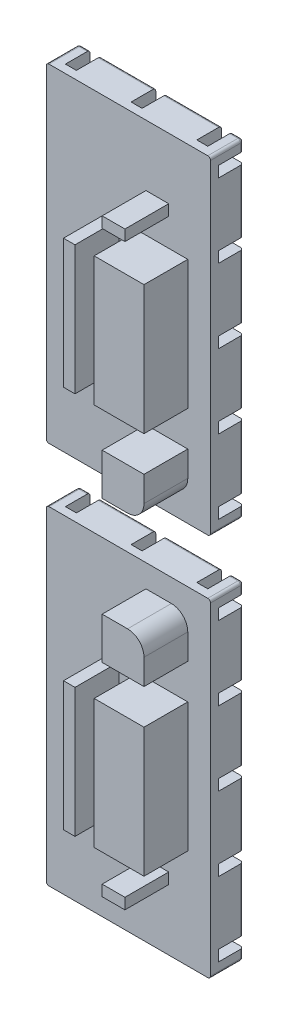
SolidWorks part; units mm, degrees
ref_plane "Front Plane" through (0, 0, 0) normal (0, 0, 1) x (1, 0, 0)
ref_plane "Top Plane" through (0, 0, 0) normal (0, 1, 0) x (1, 0, 0)
ref_plane "Right Plane" through (0, 0, 0) normal (1, 0, 0) x (0, 0, -1)
sketch "Sketch1" plane through (0, 0, 0) normal (0, 0, 1) x (1, 0, 0)
  line L1 (0, 0) -> (30, 0)
  line L2 (0, 0) -> (0, 60)
  line L3 (0, 60) -> (30, 60)
  line L4 (30, 0) -> (30, 60)
  dimension "D1" = 30
  dimension "D2" = 60
extrude "cover" add sketch "Sketch1" along normal blind 6
sketch "Sketch2" plane through (0, 0, 6) normal (0, 0, 1) x (1, 0, 0)
  line L0 (30, 60) -> (0, 60) construction
  line L1 (11.15, 55.85) -> (25.85, 55.85)
  line L2 (11.15, 55.85) -> (11.15, 11.15)
  line L3 (11.15, 11.15) -> (25.85, 11.15)
  line L4 (25.85, 55.85) -> (25.85, 11.15)
  line L6 (0, 0) -> (30, 0) construction
  line L7 (30, 0) -> (30, 60) construction
  line L8 (0, 60) -> (0, 0) construction
  dimension "D1" = 4.15
  dimension "D3" = 11.15
  dimension "D2" = 4.15
  dimension "D4" = 11.15
extrude "plug" add sketch "Sketch2" along normal blind 8
sketch "Sketch3" plane through (0, 0, 0) normal (0, 0, -1) x (-1, 0, 0)
  line L8 (0, 0) -> (-30, 0) construction
  line L10 (0, 2) -> (-30, 2)
  line L23 (0, 2) -> (0, 4)
  line L28 (0, 4) -> (-30, 4)
  line L29 (-30, 2) -> (-30, 4)
  line L34 (-30, 0) -> (-30, 60) construction
  line L40 (0, 15.5) -> (0, 17.5)
  line L41 (0, 15.5) -> (-30, 15.5)
  line L42 (-30, 15.5) -> (-30, 17.5)
  line L43 (0, 17.5) -> (-30, 17.5)
  line L44 (0, 29) -> (0, 31)
  line L45 (0, 29) -> (-30, 29)
  line L46 (-30, 29) -> (-30, 31)
  line L47 (0, 31) -> (-30, 31)
  line L48 (0, 42.5) -> (0, 44.5)
  line L49 (0, 42.5) -> (-30, 42.5)
  line L50 (-30, 42.5) -> (-30, 44.5)
  line L51 (0, 44.5) -> (-30, 44.5)
  line L52 (0, 56) -> (0, 58)
  line L53 (0, 56) -> (-30, 56)
  line L54 (-30, 56) -> (-30, 58)
  line L55 (0, 58) -> (-30, 58)
  line L58 (0, 60) -> (0, 0) construction
  dimension "D1" = 2
  dimension "D2" = 2
  dimension "D5" = 5
extrude "Cut-Extrude1" cut sketch "Sketch3" against normal blind 4.5
fillet "Fillet1" radius 3 4 edges at (11.15, 11.15, 10) (25.85, 11.15, 10) (25.85, 55.85, 10) (11.15, 55.85, 10)
sketch "Sketch4" plane through (0, 0, 6) normal (0, 0, -1) x (-1, 0, 0)
  line L0 (0, 60) -> (0, 58) construction
  line L1 (0, 48.21) -> (-9.1964, 48.21)
  line L2 (0, 48.21) -> (0, 41.79)
  line L3 (0, 41.79) -> (-11.79, 41.79)
  line L4 (-30, 48.21) -> (-30, 41.79)
  line L5 (-30, 0) -> (-30, 2) construction
  line L6 (-30, 60) -> (0, 60) construction
  line L11 (0, 0) -> (-30, 0) construction
  line L12 (-18.21, 60) -> (-11.79, 60)
  line L13 (-18.21, 60) -> (-18.21, 48.21)
  line L14 (-18.21, 0) -> (-11.79, 0)
  line L15 (-11.79, 60) -> (-11.79, 56.0154)
  line L17 (0, 18.21) -> (-11.79, 18.21)
  line L18 (0, 18.21) -> (0, 13.1449)
  line L19 (0, 13.1449) -> (-9.3197, 13.1449)
  line L20 (-30, 18.21) -> (-30, 13.1449)
  line L21 (-18.21, 48.21) -> (-30, 48.21)
  line L23 (-18.21, 41.79) -> (-30, 41.79)
  line L24 (-18.21, 18.21) -> (-30, 18.21)
  line L25 (-18.21, 13.1449) -> (-22.3683, 13.1449)
  line L26 (-18.21, 13.1449) -> (-18.21, 0)
  line L27 (-11.79, 9.6983) -> (-11.79, 0)
  line L28 (-11.79, 56.0154) -> (-9.1964, 56.0154)
  line L29 (-9.1964, 56.0154) -> (-9.1964, 48.21)
  line L30 (-16.75, 41.79) -> (-18.21, 41.79)
  line L32 (-16.75, 41.79) -> (-16.75, 18.21)
  line L34 (-13.25, 41.79) -> (-13.25, 18.21)
  line L35 (-13.25, 41.79) -> (-11.79, 41.79)
  line L36 (-16.75, 18.21) -> (-18.21, 18.21)
  line L37 (-11.79, 18.21) -> (-13.25, 18.21)
  line L38 (-30, 15) -> (0, 15) construction
  line L39 (-30, 0) -> (-30, 60) construction
  line L40 (0, 60) -> (0, 0) construction
  line L41 (-26.8003, 13.1449) -> (-26.8003, 9.5643)
  line L42 (-26.8003, 9.5643) -> (-22.3683, 9.5643)
  line L43 (-22.3683, 9.5643) -> (-22.3683, 13.1449)
  line L44 (-26.8003, 13.1449) -> (-30, 13.1449)
  line L45 (-9.3197, 13.1449) -> (-11.79, 9.6983)
  point P8 (0, 45)
  point P21 (-15, 60)
  point P42 (-30, 45)
  dimension "D1" = 15
  dimension "D2" = 6.42
  dimension "D4" = 15
  dimension "D5" = 6.42
  dimension "D3" = 26.79
  dimension "D6" = 2.5936
  dimension "D7" = 7.8054
  dimension "D8" = 3.5
  dimension "D9" = 30
  dimension "D10" = 4.4319
  dimension "D11" = 3.5806
extrude "Cut-Extrude2" cut sketch "Sketch4" against normal up to surface (8 mm away) up to face at (18.5, 33.5, 14)
sketch "Sketch5" plane through (0, 0, 0) normal (0, 0, -1) x (-1, 0, 0)
  line L13 (-30, 60) -> (0, 60) construction
  line L14 (-28, 60) -> (-26, 60)
  line L15 (-28, 60) -> (-28, 0)
  line L16 (-28, 0) -> (-26, 0)
  line L17 (-26, 60) -> (-26, 0)
  line L18 (0, 0) -> (-30, 0) construction
  line L19 (-30, 44.5) -> (-30, 56) construction
  line L20 (-16, 60) -> (-16, 0)
  line L21 (-16, 60) -> (-14, 60)
  line L22 (-14, 60) -> (-14, 0)
  line L23 (-16, 0) -> (-14, 0)
  line L24 (-4, 60) -> (-4, 0)
  line L25 (-4, 60) -> (-2, 60)
  line L26 (-2, 60) -> (-2, 0)
  line L27 (-4, 0) -> (-2, 0)
  dimension "D1" = 2
  dimension "D2" = 2
  dimension "D3" = 3
extrude "Cut-Extrude3" cut sketch "Sketch5" against normal up to surface (4.5 mm away) up to face at (15, 57, 4.5)
fillet "Fillet2" radius 0.5 24 edges at (30, 9.75, 0) (30, 23.25, 0) (30, 36.75, 0) (30, 50.25, 0) (30, 59, 0) (29, 60, 0) (21, 60, 0) (9, 60, 0) (0, 60, 3) (1, 60, 0) (0, 59, 0) (0, 50.25, 0) (0, 36.75, 0) (0, 23.25, 0) (0, 9.75, 0) (0, 1, 0) (1, 0, 0) (9, 0, 0) (21, 0, 0) (29, 0, 0) (0, 0, 3) (30, 0, 3) (30, 1, 0) (30, 60, 3)
ref_plane "Plane1" through (0, 65, 0) normal (0, 1, 0) x (1, 0, 0)
sketch "Sketch6" plane through (0, 0, 0) normal (0, 0, -1) x (-1, 0, 0)
  line L0 (-2, 0.5) -> (-2, 2) construction
  line L1 (-2, 2) -> (-0.5, 2) construction
  circle A0 centre (-1.25, 1.25) radius 0.4087
  point P6 (-2, 1.25)
  point P11 (-1.25, 2)
  dimension "D1" = 0
  dimension "D2" = 0
extrude "Cut-Extrude4" cut sketch "Sketch6" against normal blind 0.2
mirror "Mirror3" about plane through (0, 65, 0) normal (0, 1, 0) of bodies 109
equation "\"cubeCham\" = 0.7mm"
equation "\"D1@Sketch1\"=\"cleatSpacing\""
equation "\"D2@Sketch1\"=\"cleatSpacing\"*2"
equation "\"D1@cover\"=3mm"
equation "\"D1@Sketch2\" = \"wall2\""
equation "\"D3@Sketch2\" = \"cleatLen\" + \"wall2\""
equation "\"D1@plug\"=8mm"
equation "\"cleatShaftLen\" = 3"
equation "\"cleatHeadLen\" = 4mm"
equation "\"cleatHeadGirth\" = 12mm"
equation "\"cleatShaftGirth\" = 8mm"
equation "\"cleatTolOffset\" = 0.4mm"
equation "\"cleatCham\" = 1mm"
equation "\"cleatSpacing\" = 30mm"
equation "\"cleatTriangleAngle\" = 25deg"
equation "\"cleatMinimumTriangleAngle\" = 12deg"
equation "\"nCleats\" = 2"
equation "\"threadID\" = 8.3mm"
equation "\"threadPitch\" = 2mm"
equation "\"threadOD\" = 10.7mm"
equation "\"threadMaleOD\" = 10.0mm"
equation "\"cleatFemShaftLen\" = \"cleatShaftLen\" - \"cleatTolOffset\""
equation "\"cleatFemHeadLen\" = \"cleatHeadLen\" + \"cleatTolOffset\" * 1.25"
equation "\"cleatFemHeadGirth\" = \"cleatHeadGirth\" + \"cleatTolOffset\""
equation "\"cleatFemShaftGirth\" = \"cleatShaftGirth\" + \"cleatTolOffset\""
equation "\"lip\" = 2mm"
equation "\"cubeCutoutPadding\" = 3mm"
equation "\"wall\" = 3mm"
equation "\"wall2\" = 4.15mm"
equation "\"cleatLen\" = \"cleatShaftLen\" + \"cleatHeadLen\""
equation "\"coverThickness\" = 6mm"
equation "\"plugDepth\" = 8mm"
equation "\"bottomChamOffset\" = 1.8mm"
equation "\"maleHelperAngle\" = 45deg"
equation "\"maleHelperAngle2\" = 35deg"
equation "\"stFactor\" = 0.6"
equation "\"stID\" = \"threadID\" * \"stFactor\""
equation "\"stOD\" = \"threadOD\" * \"stFactor\""
equation "\"stPitch\" = \"threadPitch\" * \"stFactor\""
equation "\"stProtrusion\" = (\"stOD\" - \"stID\") / 2"
equation "\"stMaleOD\" = \"threadMaleOD\" * \"stFactor\""
equation "\"stHexDiam\" = 2.5mm"
equation "\"stHexPad\" = 0.08mm"
equation "\"stSocketHeadProtrusion\" = 0.65mm"
equation "\"stSocketHeadDiam\" = \"stOD\" + \"stSocketHeadProtrusion\""
equation "\"stSocketHeadLen\" = 1.2mm"
equation "\"stSocketHeadLenPad\" = 0.1mm"
equation "\"stSocketHeadCounterboreDepth\" = \"stSocketHeadLen\" + \"stSocketHeadLenPad\""
equation "\"stDriverDepth\" = 2mm"
equation "\"stNutODPad\" = 3mm"
equation "\"stNutDiam\" = \"stOD\" + \"stNutODPad\""
equation "\"stNutHeight\" = 3mm"
equation "\"stNutCham\" = 0.4mm"
equation "\"temp\" = 0"
equation "\"plugCornerFill\" = 3mm"
equation "\"D1@Fillet1\"=\"plugCornerFill\""
equation "\"D4@Sketch2\"=\"cleatLen\"+\"wall2\""
equation "\"D2@Sketch2\"=\"wall2\""
equation "\"D5@Sketch4\"=\"stOD\""
equation "\"D3@Sketch4\"=30mm-\"stOD\"/2"
